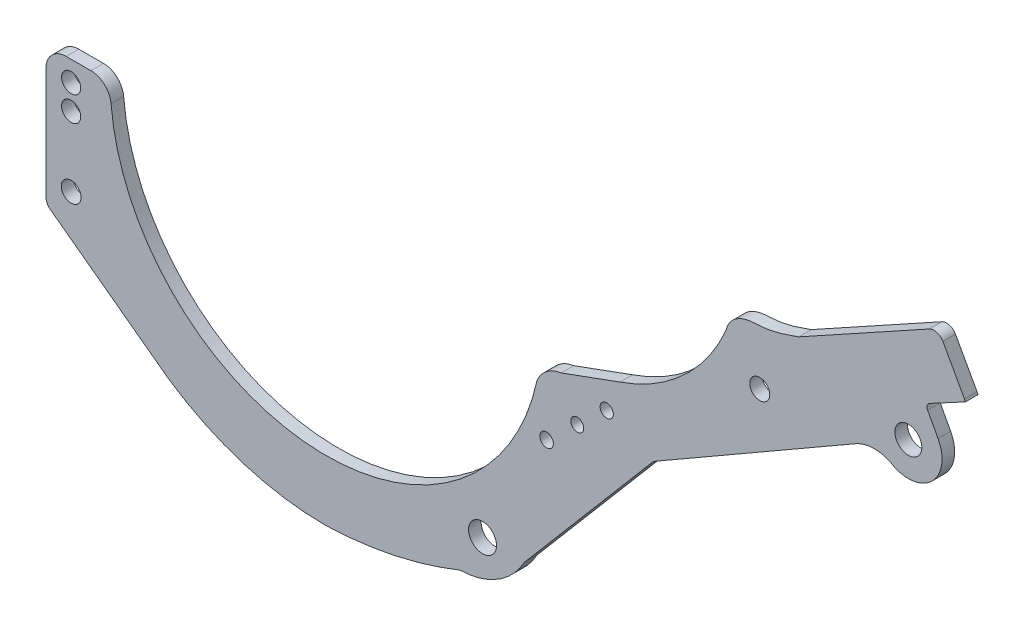
SolidWorks part; units mm, degrees
ref_plane "Plano frontal" through (0, 0, 0) normal (0, 0, 1) x (1, 0, 0)
ref_plane "Plano superior" through (0, 0, 0) normal (0, 1, 0) x (1, 0, 0)
ref_plane "Plano direito" through (0, 0, 0) normal (1, 0, 0) x (0, 0, -1)
sketch "Esboço1" plane through (0, 0, 0) normal (0, 0, 1) x (1, 0, 0)
  line L0 (341.3333, 723.5) -> (1706.6667, 723.5) construction
  line L1 (4411.2884, 5118.4934) -> (4368.5281, 5195.9331)
  line L2 (4341.3522, 5203.7736) -> (4082.3803, 5060.7754)
  line L3 (3728.4625, 4806.151) -> (3611.0666, 4763.1916)
  line L4 (2678.7395, 4816.1158) -> (2629.6227, 4816.1158)
  line L5 (2597.7164, 4537.8387) -> (2798.6248, 4388.9824)
  line L6 (3538.4433, 4401.4915) -> (3794.4879, 4702.9043)
  line L7 (2589.6227, 4553.9085) -> (2589.6227, 4776.1158)
  line L8 (3794.4879, 4702.9043) -> (4192.1494, 4931.8856)
  line L9 (4358.8604, 5024.3409) -> (4338.2041, 5062.9282)
  line L10 (4342.3009, 5076.4639) -> (4413.1142, 5114.3712)
  line L11 (4413.1142, 5114.3712) -> (4411.2884, 5118.4934)
  arc A0 (3728.4625, 4806.151) -> (3939.0141, 5001.5801) centre (3615.5351, 5138.9536) ccw
  arc A1 (3611.0666, 4763.1916) -> (3563.5197, 4726.7183) centre (3619.5503, 4702.9043) ccw
  arc A2 (2718.5931, 4779.5348) -> (3563.5197, 4726.7183) centre (3144.9939, 4816.1158) ccw
  arc A3 (2589.6227, 4776.1158) -> (2629.6227, 4816.1158) centre (2629.6227, 4776.1158) cw
  arc A4 (2678.7395, 4816.1158) -> (2718.5931, 4779.5348) centre (2678.7395, 4776.1158) cw
  arc A5 (2798.6248, 4388.9824) -> (3144.9939, 4267.8722) centre (3144.7865, 4823.1328) ccw
  arc A6 (3410.5618, 4324.2586) -> (3538.4433, 4401.4915) centre (3408.3095, 4472.4768) ccw
  circle A7 centre (4299.9789, 4992.8208) radius 26.7155
  arc A8 (4263.3618, 4936.9663) -> (4358.8604, 5024.3409) centre (4299.9789, 4992.8208) ccw
  arc A9 (4192.1494, 4931.8856) -> (4272.6394, 4931.8856) centre (4232.3944, 4869.4064) cw
  arc A10 (4338.2041, 5062.9282) -> (4342.3009, 5076.4639) centre (4347.0204, 5067.6476) cw
  circle A11 centre (4005.2379, 4932.681) radius 19.8494
  circle A12 centre (3701.6895, 4743.8762) radius 13.1837
  circle A13 centre (3582.4369, 4633.88) radius 13.5034
  circle A14 centre (3643.3118, 4690.4842) radius 12.8481
  circle A15 centre (2639.499, 4776.1158) radius 19
  circle A16 centre (3455.3928, 4402.5824) radius 27.7134
  circle A17 centre (2639.499, 4726.7183) radius 19
  circle A18 centre (2639.499, 4588.6344) radius 19.6429
  arc A19 (2597.7164, 4537.8387) -> (2589.6227, 4553.9085) centre (2609.6227, 4553.9085) cw
  arc A20 (4368.5281, 5195.9331) -> (4341.3522, 5203.7736) centre (4351.0199, 5186.2654) ccw
  spline S0 degree 3 poles (4082.3803, 5060.7754) (4060.6533, 5053.0503) (4026.4586, 5040.4172) (3971.3833, 5041.9754) (3943.2043, 5021.3899) (3939.0141, 5001.5801) knots 0 0 0 0 0.42893 0.656274 1 1 1 1
  spline S1 degree 2 poles (3144.9939, 4267.8722) (3283.0879, 4272.5243) (3410.5618, 4324.2586) knots 0 0 0 1 1 1
  point P6 (3728.4625, 4806.151)
  point P19 (3144.9939, 4816.1158)
  point P22 (2589.6227, 4816.1158)
  point P26 (2717.0269, 4816.1158)
  point P27 (3144.9939, 4267.8722)
  point P47 (4333.4847, 5071.7444)
  point P66 (2589.6227, 4543.8354)
  point P69 (4358.8604, 5213.4413)
  dimension "D3" = 125.0093
  dimension "D4" = 40
  dimension "D5" = 260.1179
  dimension "D6" = 395.4852
  dimension "D9" = 53.7682
  dimension "D12" = 10
  dimension "D13" = 20
  dimension "D14" = 20
  dimension "D1" = 108.461
  dimension "D2" = 315.8293
  dimension "D7" = 272.2804
  dimension "D8" = 458.8759
  dimension "D10" = 90.3211
  dimension "D11" = 4.5084
extrude "Ressalto-extrusão1" add sketch "Esboço1" along normal blind 25 contours A5 S1 A6 L6 L8 A9 A8 L9 A10 L10 L11 L1 A20 L2 S0 A0 L3 A1 A2 A4 L4 A3 L7 A19 L5 A7 A11 A12 A13 A14 A15 A16 A17 A18
